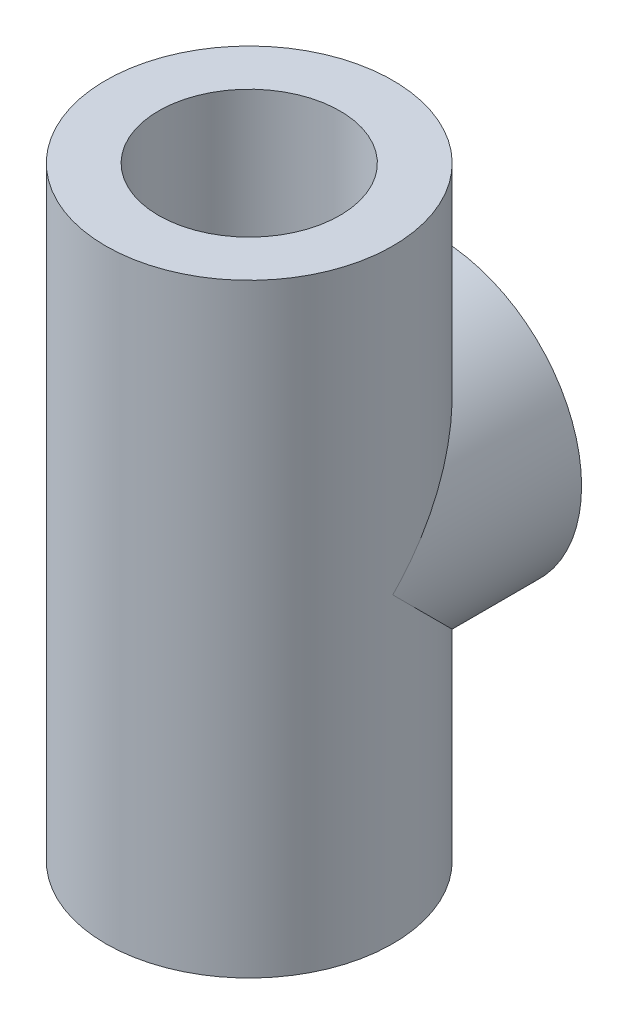
SolidWorks part; units mm, degrees
ref_plane "Front Plane" through (0, 0, 0) normal (0, 0, 1) x (1, 0, 0)
ref_plane "Top Plane" through (0, 0, 0) normal (0, 1, 0) x (1, 0, 0)
ref_plane "Right Plane" through (0, 0, 0) normal (1, 0, 0) x (0, 0, -1)
sketch "Sketch1" plane through (0, 0, 0) normal (0, 1, 0) x (1, 0, 0)
  circle A0 centre (0, 0) radius 30
  circle A1 centre (0, 0) radius 47.5
  dimension "D1" = 60
  dimension "D2" = 95
extrude "Boss-Extrude1" add sketch "Sketch1" along normal blind 200
ref_plane "Plane1" through (0, 0, -62.5) normal (0, 0, 1) x (1, 0, 0)
sketch "Sketch2" plane through (0, 0, -62.5) normal (0, 0, 1) x (1, 0, 0)
  line L0 (0, 0) -> (0, 200) construction
  line L1 (-47.5, 0) -> (47.5, 0) construction
  line L2 (47.5, 200) -> (-47.5, 200) construction
  line L3 (0, 200) -> (0, 100) construction
  line L4 (0, 100) -> (47.5, 100) construction
  line L5 (47.5, 0) -> (47.5, 200) construction
  circle A0 centre (0, 100) radius 47.5
  circle A1 centre (0, 100) radius 27
  dimension "D1" = 95
  dimension "D2" = 54
extrude "Boss-Extrude2" add sketch "Sketch2" along normal up to next contours A1 | A0 A1
sketch "Sketch3" plane through (0, 0, -62.5) normal (0, 0, -1) x (-1, 0, 0)
  circle A0 centre (0, 100) radius 27
  dimension "D1" = 54
extrude "Cut-Extrude1" cut sketch "Sketch3" against normal blind 4 and the other way through all
sketch "Sketch4" plane through (0, 0, -62.5) normal (0, 0, -1) x (-1, 0, 0)
  circle A0 centre (0, 100) radius 38 construction
  circle A1 centre (0, 138) radius 5
  circle A2 centre (38, 100) radius 5
  circle A3 centre (0, 62) radius 5
  circle A4 centre (-38, 100) radius 5
  point P4 (0, 138)
  point P6 (-38, 100)
  point P8 (0, 62)
  point P10 (38, 100)
  point P26 (0, 100)
  dimension "D1" = 76
  dimension "D2" = 10
  dimension "D3" = 4
extrude "Cut-Extrude2" cut sketch "Sketch4" against normal blind 20
